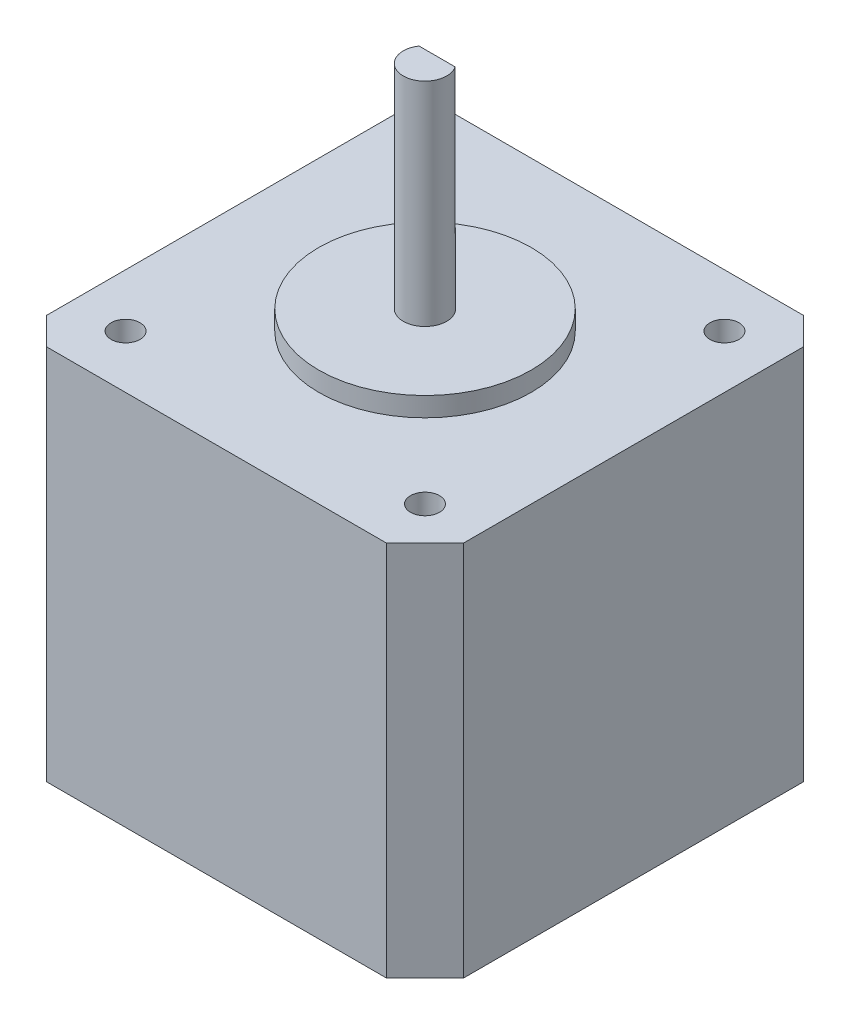
SolidWorks part; units mm, degrees
ref_plane "Front Plane" through (0, 0, 0) normal (0, 0, 1) x (1, 0, 0)
ref_plane "Top Plane" through (0, 0, 0) normal (0, 1, 0) x (1, 0, 0)
ref_plane "Right Plane" through (0, 0, 0) normal (1, 0, 0) x (0, 0, -1)
sketch "Sketch1" plane through (0, 0, 0) normal (0, 1, 0) x (1, 0, 0)
  line L0 (-21, 18.1716) -> (-18.1716, 21)
  line L1 (-18.1716, 21) -> (18.1716, 21)
  line L2 (-21, 18.1716) -> (-21, -18.1716)
  line L3 (-18.1716, -21) -> (17, -21)
  line L4 (21, 18.1716) -> (21, -17)
  line L5 (-19.5858, 19.5858) -> (19, -19) construction
  line L6 (-19.5858, -19.5858) -> (19.5858, 19.5858) construction
  line L7 (18.1716, 21) -> (21, 18.1716)
  line L8 (21, -17) -> (17, -21)
  line L9 (-18.1716, -21) -> (-21, -18.1716)
  point P0 (0, 0)
  dimension "D3" = 4
  dimension "D4" = 4
  dimension "D5" = 4
  dimension "D6" = 4
  dimension "D7" = 45
  dimension "D8" = 45
  dimension "D9" = 45
  dimension "D10" = 45
extrude "Boss-Extrude1" add sketch "Sketch1" along normal blind 39
sketch "Sketch2" plane through (0, 39, 0) normal (0, 1, 0) x (1, 0, 0)
  circle A0 centre (0, 0) radius 2.25
  dimension "D1" = 4.5
extrude "Boss-Extrude2" add sketch "Sketch2" along normal blind 24
sketch "Sketch3" plane through (0, 39, 0) normal (0, 1, 0) x (1, 0, 0)
  circle A0 centre (0, 0) radius 11
  dimension "D1" = 22
extrude "Boss-Extrude3" add sketch "Sketch3" along normal blind 2
sketch "Sketch4" plane through (0, 39, 0) normal (0, 1, 0) x (1, 0, 0)
  line L0 (-21, 18.1716) -> (-21, -18.1716) construction
  line L2 (18.1716, 21) -> (-18.1716, 21) construction
  circle A0 centre (-15.5, 15.5) radius 1.5
  circle A1 centre (15.5, 15.5) radius 1.5
  dimension "D1" = 3
  dimension "D2" = 3
  dimension "D3" = 31
  dimension "D4" = 5.5
  dimension "D5" = 5.5
extrude "Cut-Extrude1" cut sketch "Sketch4" against normal blind 4.5
mirror "Mirror1" about plane through (0, 0, 0) normal (0, 0, 1) of "Cut-Extrude1"
sketch "Sketch5" plane through (0, 63, 0) normal (0, 1, 0) x (1, 0, 0)
  line L0 (1.8708, 1.25) -> (-1.8708, 1.25)
  circle A0 centre (0, 0) radius 2.25 construction
  arc A1 (-1.8708, 1.25) -> (1.8708, 1.25) centre (0, 0) cw
  dimension "D1" = 3.5
extrude "Cut-Extrude2" cut sketch "Sketch5" against normal blind 15
